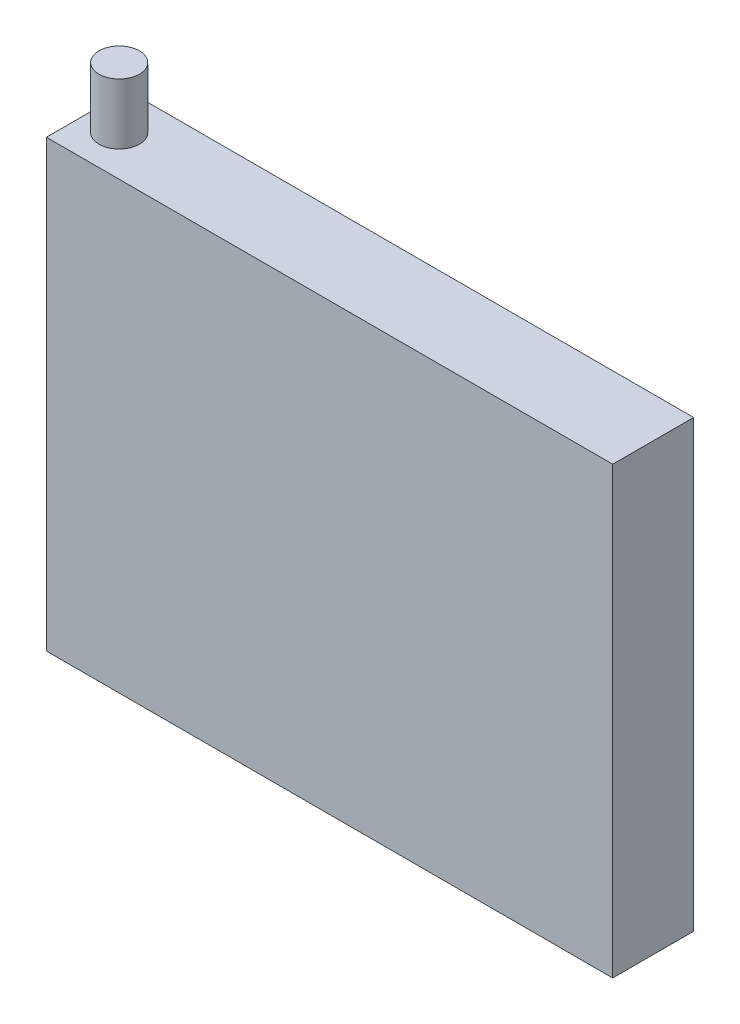
SolidWorks part; units mm, degrees
ref_plane "Front Plane" through (0, 0, 0) normal (0, 0, 1) x (1, 0, 0)
ref_plane "Top Plane" through (0, 0, 0) normal (0, 1, 0) x (1, 0, 0)
ref_plane "Right Plane" through (0, 0, 0) normal (1, 0, 0) x (0, 0, -1)
sketch "Sketch1" plane through (0, 0, 0) normal (0, 0, 1) x (1, 0, 0)
  line L1 (-35, -27.5) -> (35, -27.5)
  line L2 (-35, -27.5) -> (-35, 27.5)
  line L3 (-35, 27.5) -> (35, 27.5)
  line L4 (35, -27.5) -> (35, 27.5)
  line L5 (-35, -27.5) -> (35, 27.5) construction
  line L6 (-35, 27.5) -> (35, -27.5) construction
  point P0 (0, 0)
  dimension "D1" = 55
  dimension "D2" = 70
extrude "Boss-Extrude1" add sketch "Sketch1" along normal blind 10
sketch "Sketch2" plane through (0, 0, 0) normal (0, 1, 0) x (1, 0, 0)
  line L0 (-35, -5) -> (35, -5) construction
  line L1 (-35, -10) -> (-35, 0) construction
  line L2 (35, -10) -> (35, 0) construction
  circle A0 centre (-31, -5) radius 2.5
  dimension "D1" = 5
  dimension "D2" = 4
extrude "Boss-Extrude2" add sketch "Sketch2" along normal mid plane 70
sketch "Sketch3" plane through (0, -35, 0) normal (0, -1, 0) x (1, 0, 0)
  circle A0 centre (-31, 5) radius 2.5
extrude "Cut-Extrude1" cut sketch "Sketch3" against normal blind 10
